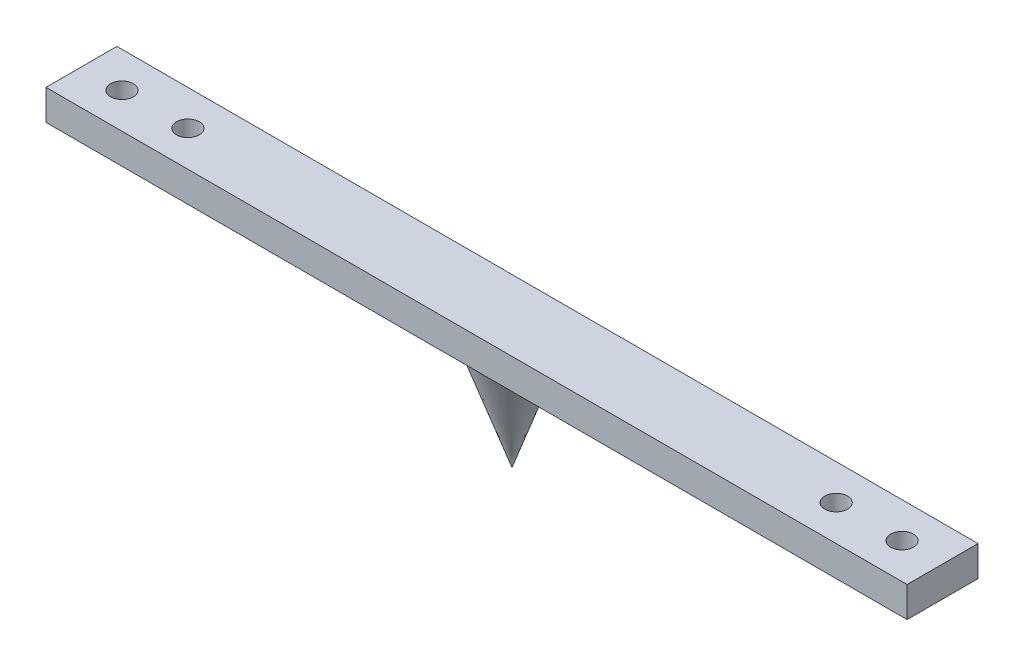
SolidWorks part; units mm, degrees
ref_plane "Ebene vorne" through (0, 0, 0) normal (0, 0, 1) x (1, 0, 0)
ref_plane "Ebene oben" through (0, 0, 0) normal (0, 1, 0) x (1, 0, 0)
ref_plane "Ebene rechts" through (0, 0, 0) normal (1, 0, 0) x (0, 0, -1)
sketch "Skizze1" plane through (0, 0, 0) normal (0, 1, 0) x (1, 0, 0)
  line L0 (-85, 0) -> (85, 0) construction
  line L1 (-85, 7) -> (85, 7)
  line L2 (-85, 7) -> (-85, -7)
  line L3 (-85, -7) -> (85, -7)
  line L4 (85, 7) -> (85, -7)
  line L5 (0, 7) -> (0, -7) construction
  point P8 (0, 0)
  dimension "D1" = 14
  dimension "D2" = 170
extrude "Aufsatz-Linear austragen1" add sketch "Skizze1" along normal blind 6
hole_wizard "Stirnsenkung für M4 Senkschraube (Kopf Button)1" positions "3D-Skizze1" profile "Skizze2" counterbore size "M4" standard "ANSI Metrisch"
sketch3d "3D-Skizze1"
  line L0 (-85, 0, 0) -> (85, 0, 0) construction
  line L1 (-85, 0, -7) -> (-85, 0, 7) construction
  line L2 (85, 0, 7) -> (85, 0, -7) construction
  line L3 (0, 0, 0) -> (0, 0, -36.1281) construction
  point P0 (-77, 0, 0)
  point P2 (-64, 0, 0)
  point P4 (64, 0, 0)
  point P6 (77, 0, 0)
  point P21 (0, 0, 0)
  dimension "D1" = 13
  dimension "D2" = 13
  dimension "D3" = 128
  dimension "D4" = 64
sketch "Skizze2" plane through (-77, 0, 0) normal (1, 0, 0) x (0, 0, -1)
  line L0 (0, 0) -> (0, 6)
  line L1 (0, 6) -> (2.25, 6)
  line L3 (2.25, 6) -> (2.25, 2.2)
  line L4 (2.25, 2.2) -> (4, 2.2)
  line L5 (4, 2.2) -> (4, 0)
  line L7 (4, 0) -> (0, 0)
  line L11 (0, -6.35) -> (0, 107.95) construction
  dimension "Bohrerdurchmesser" = 4.5
  dimension "Bohrungstiefe" = 6
  dimension "Senkdurchmesser2" = 8
  dimension "Senktiefe2" = 2.2
ref_plane "Ebene1" through (0, 0, 0) normal (0, 0, 1) x (1, 0, 0)
sketch "Skizze3" plane through (0, 0, 0) normal (0, 0, 1) x (1, 0, 0)
  line L0 (0, 32.9612) -> (0, -31.0486) construction
  line L1 (-7, 0) -> (0, -20)
  line L4 (0, 0) -> (-7, 0)
  line L5 (0, -20) -> (0, 0)
  dimension "D1" = 20
  dimension "D2" = 7
revolve "Rotation1" add sketch "Skizze3" angle 360 about L0
